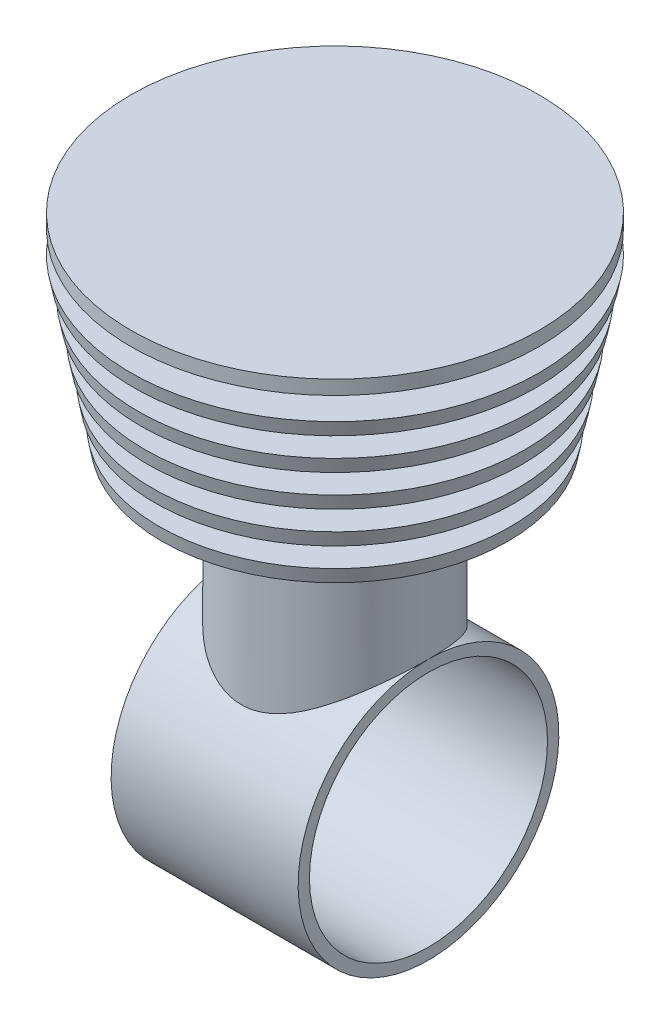
SolidWorks part; units mm, degrees
ref_plane "Plan de face" through (0, 0, 0) normal (0, 0, 1) x (1, 0, 0)
ref_plane "Plan de dessus" through (0, 0, 0) normal (0, 1, 0) x (1, 0, 0)
ref_plane "Plan de droite" through (0, 0, 0) normal (1, 0, 0) x (0, 0, -1)
sketch "Esquisse1" plane through (0, 0, 0) normal (0, 0, 1) x (1, 0, 0)
  line L0 (-16.5, 0) -> (16.5, 0)
  line L1 (16.5, 0) -> (16.5, -2)
  line L2 (16.5, -2) -> (-16.5, -2)
  line L3 (-16.5, -2) -> (-16.5, 0)
  line L4 (0, 0) -> (0, -23) construction
  line L5 (0, -23) -> (10.3629, -23) construction
  point P4 (0, 0)
  dimension "D1" = 33
  dimension "D2" = 2
  dimension "D3" = 21
revolve "Révolution1" add sketch "Esquisse1" angle 360 about L5
sketch "Esquisse2" plane through (0, 0, 0) normal (0, 0, 1) x (1, 0, 0)
  line L0 (-16.5, 0) -> (-16.5, 25)
  line L1 (-16.5, 25) -> (-36, 25)
  line L2 (-36, 25) -> (-36, 27.5)
  line L3 (-36, 27.5) -> (-16.5, 27.5)
  line L4 (-16.5, 27.5) -> (-16.5, 31.5)
  line L5 (-16.5, 31.5) -> (-36, 31.5)
  line L6 (-36, 31.5) -> (-36, 34)
  line L7 (-36, 34) -> (-16.5, 34)
  line L8 (-16.5, 34) -> (-16.5, 38)
  line L9 (-16.5, 38) -> (-36, 38)
  line L10 (-36, 38) -> (-36, 40.5)
  line L11 (-36, 40.5) -> (-23.5, 40.5)
  line L12 (-23.5, 40.5) -> (-23.5, 44.5)
  line L13 (-23.5, 44.5) -> (-36, 44.5)
  line L14 (-36, 44.5) -> (-36, 47)
  line L15 (-36, 47) -> (-23.5, 47)
  line L16 (-23.5, 47) -> (-23.5, 51)
  line L17 (-23.5, 51) -> (-36, 51)
  line L18 (-36, 51) -> (-36, 53.5)
  line L19 (-36, 53.5) -> (-23.5, 53.5)
  line L20 (-23.5, 53.5) -> (-23.5, 57.5)
  line L21 (-23.5, 57.5) -> (-36, 57.5)
  line L22 (-36, 57.5) -> (-36, 60)
  line L23 (-36, 60) -> (0, 60)
  line L24 (0, 60) -> (0, 56)
  line L25 (0, 56) -> (-13.5, 56)
  line L26 (-13.5, 56) -> (-13.5, 0)
  line L27 (16.5, 0) -> (-16.5, 0) construction
  line L28 (-13.5, 0) -> (-16.5, 0)
  line L29 (0, 56) -> (0, 0) construction
  dimension "D1" = 25
  dimension "D2" = 2.5
  dimension "D3" = 2.5
  dimension "D4" = 2.5
  dimension "D5" = 2.5
  dimension "D6" = 2.5
  dimension "D7" = 2.5
  dimension "D8" = 60
  dimension "D9" = 3
  dimension "D11" = 10
  dimension "D12" = 4
  dimension "D13" = 36
  dimension "D27" = 13.5
revolve "Révolution2" add sketch "Esquisse2" angle 360 about L29
sketch "Esquisse4" plane through (0, 0, 0) normal (0, 0, 1) x (1, 0, 0)
  line L0 (-36, 60) -> (-36, 53.5)
  line L1 (36, 53.5) -> (-36, 53.5) construction
  line L2 (-36, 53.5) -> (-30.5, 25)
  line L3 (-36, 25) -> (36, 25) construction
  line L4 (-30.5, 25) -> (-37, 25)
  line L5 (-37, 25) -> (-37, 60)
  line L6 (-37, 60) -> (-36, 60)
  line L7 (0, 0) -> (0, 61.7482) construction
  dimension "D1" = 14
  dimension "D2" = 1
revolve "Enlèvement de matière-Révolution1" cut sketch "Esquisse4" angle 360 about L7
sketch "Esquisse5" plane through (0, 0, 0) normal (0, -1, 0) x (1, 0, 0)
  circle A0 centre (0, 0) radius 16.5 construction
  circle A1 centre (0, 0) radius 13.5 construction
  circle A2 centre (0, 0) radius 16.5
  circle A3 centre (0, 0) radius 13.5
extrude "Boss.-Extru.1" add sketch "Esquisse5" along normal up to body separate body
sketch "Esquisse6" plane through (0, 0, 0) normal (0, 1, 0) x (1, 0, 0)
  circle A0 centre (0, 0) radius 13.5
  dimension "D1" = 27
extrude "Enlèv. mat.-Extru.1" cut sketch "Esquisse6" against normal up to next
sketch "Esquisse7" plane through (16.5, 0, 0) normal (1, 0, 0) x (0, 0, -1)
